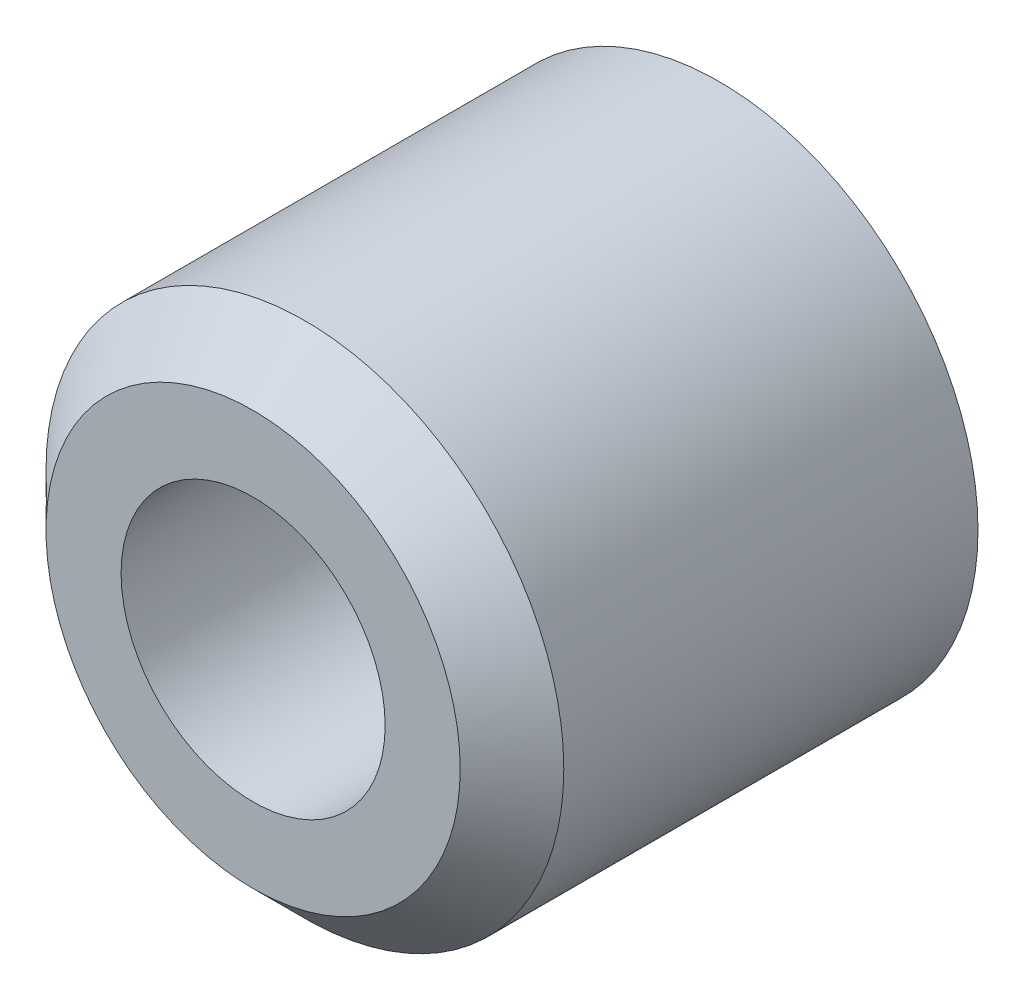
SolidWorks part; units mm, degrees
material "6061-T6 (SS)"
ref_plane "Спереди" through (0, 0, 0) normal (0, 0, 1) x (1, 0, 0)
ref_plane "Сверху" through (0, 0, 0) normal (0, 1, 0) x (1, 0, 0)
ref_plane "Справа" through (0, 0, 0) normal (1, 0, 0) x (0, 0, -1)
sketch "Эскиз1" plane through (0, 0, 0) normal (0, 0, 1) x (1, 0, 0)
  circle A0 centre (0, 0) radius 5
  circle A1 centre (0, 0) radius 2.55
  dimension "D1" = 10
  dimension "D2" = 5.1
extrude "Base" add sketch "Эскиз1" along normal blind 9
chamfer "Chamfer1" distance 1 angle 45 1 edges at (5, 0, 9)
